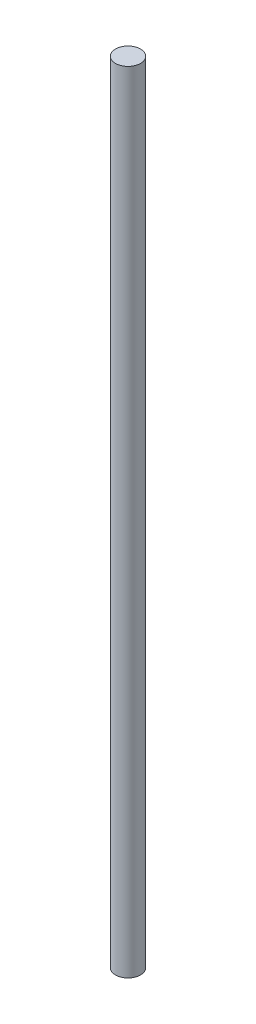
SolidWorks part; units mm, degrees
ref_plane "Front Plane" through (0, 0, 0) normal (0, 0, 1) x (1, 0, 0)
ref_plane "Top Plane" through (0, 0, 0) normal (0, 1, 0) x (1, 0, 0)
ref_plane "Right Plane" through (0, 0, 0) normal (1, 0, 0) x (0, 0, -1)
sketch "Sketch1" plane through (0, 0, 0) normal (0, 1, 0) x (1, 0, 0)
  circle A0 centre (0, 0) radius 0.95
  dimension "D1" = 1.9
extrude "Boss-Extrude1" add sketch "Sketch1" along normal blind 60
